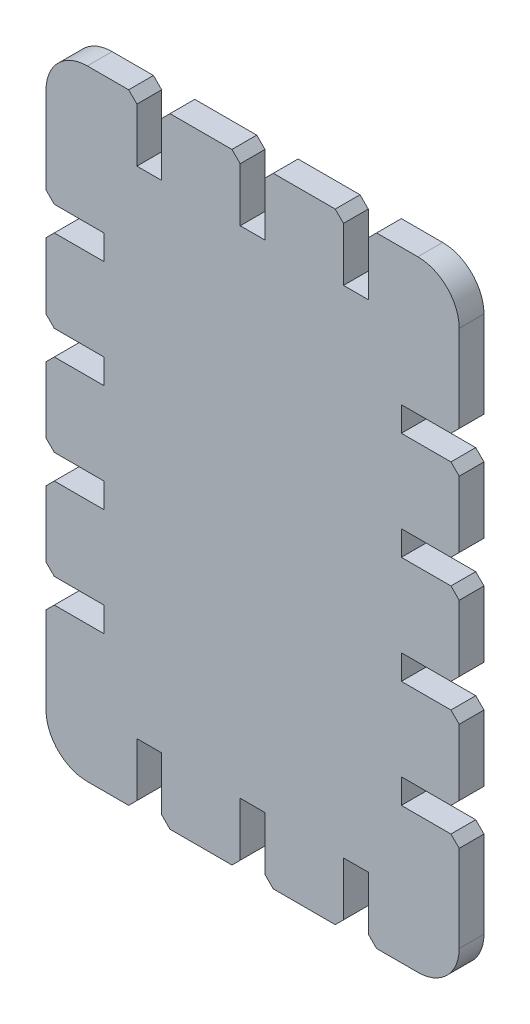
SolidWorks part; units mm, degrees
ref_plane "Front Plane" through (0, 0, 0) normal (0, 0, 1) x (1, 0, 0)
ref_plane "Top Plane" through (0, 0, 0) normal (0, 1, 0) x (1, 0, 0)
ref_plane "Right Plane" through (0, 0, 0) normal (1, 0, 0) x (0, 0, -1)
sketch "Sketch1" plane through (0, 0, 0) normal (0, 0, 1) x (1, 0, 0)
  line L0 (-5.5, 27.6932) -> (-5.5, -47.3068) construction
  line L1 (-15.5, 27.6932) -> (-8, 27.6932)
  line L2 (-25.5, -47.3068) -> (-20.5, -47.3068)
  line L3 (-30.5, -42.3068) -> (-30.5, -31.8068)
  line L4 (-25.5, 27.6932) -> (-20.5, 27.6932)
  line L5 (19.5, -42.3068) -> (19.5, -31.8068)
  line L6 (-30.5, -47.3068) -> (19.5, 27.6932) construction
  line L7 (-30.5, 27.6932) -> (19.5, -47.3068) construction
  line L8 (-16.5, 20.1932) -> (-19.5, 20.1932)
  line L9 (-16.5, 20.1932) -> (-16.5, 26.6932)
  line L10 (-20.5, 27.6932) -> (-19.5, 26.6932)
  line L11 (-19.5, 20.1932) -> (-19.5, 26.6932)
  line L12 (-16.5, 26.6932) -> (-15.5, 27.6932)
  line L13 (-4, 20.1932) -> (-7, 20.1932)
  line L14 (-4, 20.1932) -> (-4, 26.6932)
  line L15 (-7, 20.1932) -> (-7, 26.6932)
  line L16 (-8, 27.6932) -> (-7, 26.6932)
  line L17 (-4, 26.6932) -> (-3, 27.6932)
  line L18 (8.5, 20.1932) -> (5.5, 20.1932)
  line L19 (8.5, 20.1932) -> (8.5, 26.6932)
  line L20 (5.5, 20.1932) -> (5.5, 26.6932)
  line L21 (4.5, 27.6932) -> (5.5, 26.6932)
  line L22 (8.5, 26.6932) -> (9.5, 27.6932)
  line L23 (-3, 27.6932) -> (4.5, 27.6932)
  line L24 (9.5, 27.6932) -> (14.5, 27.6932)
  line L25 (12.5, 11.1932) -> (18.5, 11.1932)
  line L26 (12.5, 11.1932) -> (12.5, 8.1932)
  line L27 (12.5, 8.1932) -> (18.5, 8.1932)
  line L28 (19.5, 12.1932) -> (19.5, 22.6932)
  line L29 (18.5, 11.1932) -> (19.5, 12.1932)
  line L30 (18.5, 8.1932) -> (19.5, 7.1932)
  line L31 (-30.5, -9.8068) -> (19.5, -9.8068) construction
  line L32 (8.5, -46.3068) -> (9.5, -47.3068)
  line L33 (4.5, -47.3068) -> (5.5, -46.3068)
  line L34 (5.5, -39.8068) -> (5.5, -46.3068)
  line L35 (8.5, -39.8068) -> (8.5, -46.3068)
  line L36 (8.5, -39.8068) -> (5.5, -39.8068)
  line L37 (-4, -46.3068) -> (-3, -47.3068)
  line L38 (-8, -47.3068) -> (-7, -46.3068)
  line L39 (-7, -39.8068) -> (-7, -46.3068)
  line L40 (-4, -39.8068) -> (-4, -46.3068)
  line L41 (-4, -39.8068) -> (-7, -39.8068)
  line L42 (-16.5, -46.3068) -> (-15.5, -47.3068)
  line L43 (-19.5, -39.8068) -> (-19.5, -46.3068)
  line L44 (-20.5, -47.3068) -> (-19.5, -46.3068)
  line L45 (-16.5, -39.8068) -> (-16.5, -46.3068)
  line L46 (-16.5, -39.8068) -> (-19.5, -39.8068)
  line L47 (-15.5, -47.3068) -> (-8, -47.3068)
  line L48 (-3, -47.3068) -> (4.5, -47.3068)
  line L49 (12.5, -1.8068) -> (18.5, -1.8068)
  line L50 (12.5, -1.8068) -> (12.5, -4.8068)
  line L51 (12.5, -4.8068) -> (18.5, -4.8068)
  line L52 (18.5, -1.8068) -> (19.5, -0.8068)
  line L53 (18.5, -4.8068) -> (19.5, -5.8068)
  line L54 (12.5, -14.8068) -> (18.5, -14.8068)
  line L55 (12.5, -14.8068) -> (12.5, -17.8068)
  line L56 (12.5, -17.8068) -> (18.5, -17.8068)
  line L57 (18.5, -14.8068) -> (19.5, -13.8068)
  line L58 (18.5, -17.8068) -> (19.5, -18.8068)
  line L59 (12.5, -27.8068) -> (18.5, -27.8068)
  line L60 (12.5, -27.8068) -> (12.5, -30.8068)
  line L61 (12.5, -30.8068) -> (18.5, -30.8068)
  line L62 (18.5, -27.8068) -> (19.5, -26.8068)
  line L63 (18.5, -30.8068) -> (19.5, -31.8068)
  line L64 (19.5, -0.8068) -> (19.5, 7.1932)
  line L65 (19.5, -13.8068) -> (19.5, -5.8068)
  line L66 (19.5, -26.8068) -> (19.5, -18.8068)
  line L67 (-23.5, -27.8068) -> (-23.5, -30.8068)
  line L68 (-23.5, -14.8068) -> (-23.5, -17.8068)
  line L69 (-23.5, -1.8068) -> (-23.5, -4.8068)
  line L70 (-29.5, 11.1932) -> (-30.5, 12.1932)
  line L71 (-23.5, 11.1932) -> (-23.5, 8.1932)
  line L72 (-23.5, 11.1932) -> (-29.5, 11.1932)
  line L73 (-29.5, -4.8068) -> (-30.5, -5.8068)
  line L74 (-29.5, -1.8068) -> (-30.5, -0.8068)
  line L75 (-23.5, -4.8068) -> (-29.5, -4.8068)
  line L76 (-23.5, -1.8068) -> (-29.5, -1.8068)
  line L77 (-29.5, 8.1932) -> (-30.5, 7.1932)
  line L78 (-23.5, 8.1932) -> (-29.5, 8.1932)
  line L79 (-29.5, -30.8068) -> (-30.5, -31.8068)
  line L80 (-29.5, -27.8068) -> (-30.5, -26.8068)
  line L81 (-23.5, -30.8068) -> (-29.5, -30.8068)
  line L82 (-23.5, -27.8068) -> (-29.5, -27.8068)
  line L83 (-29.5, -17.8068) -> (-30.5, -18.8068)
  line L84 (-29.5, -14.8068) -> (-30.5, -13.8068)
  line L85 (-23.5, -17.8068) -> (-29.5, -17.8068)
  line L86 (-23.5, -14.8068) -> (-29.5, -14.8068)
  line L87 (-30.5, 12.1932) -> (-30.5, 22.6932)
  line L88 (-30.5, -0.8068) -> (-30.5, 7.1932)
  line L89 (-30.5, -13.8068) -> (-30.5, -5.8068)
  line L90 (-30.5, -26.8068) -> (-30.5, -18.8068)
  line L91 (-18, 27.6932) -> (-18, 17.7664) construction
  line L92 (9.5, -47.3068) -> (14.5, -47.3068)
  line L93 (19.5, 9.6932) -> (12.5, 9.6932) construction
  arc A0 (14.5, -47.3068) -> (19.5, -42.3068) centre (14.5, -42.3068) ccw
  arc A1 (-25.5, -47.3068) -> (-30.5, -42.3068) centre (-25.5, -42.3068) cw
  arc A2 (19.5, 22.6932) -> (14.5, 27.6932) centre (14.5, 22.6932) ccw
  arc A3 (-30.5, 22.6932) -> (-25.5, 27.6932) centre (-25.5, 22.6932) cw
  point P0 (-5.5, -9.8068)
  point P4 (0, 0)
  point P9 (-18, 27.6932)
  point P10 (-16.5, 27.6932)
  point P14 (-19.5, 27.6932)
  point P21 (-5.5, 27.6932)
  point P22 (-4, 27.6932)
  point P26 (-7, 27.6932)
  point P30 (7, 27.6932)
  point P31 (8.5, 27.6932)
  point P35 (5.5, 27.6932)
  point P46 (19.5, 9.6932)
  point P50 (19.5, 8.1932)
  point P51 (19.5, 11.1932)
  point P121 (-18, 20.1932)
  point P124 (12.5, -29.3068)
  dimension "D3" = 5
  dimension "D1" = 3
  dimension "D2" = 12.5
  dimension "D4" = 18
  dimension "D5" = 4
  dimension "D6" = 3
  dimension "D11" = 3
  dimension "D12" = 18
extrude "Boss-Extrude1" add sketch "Sketch1" along normal blind 3 contours L87 A3 L4 L10 L11 L8 L9 L12 L1 L16 L15 L13 L14 L17 L23 L21 L20 L18 L19 L22 L24 A2 L28 L29 L25 L26 L27 L30 L64 L52 L49 L50 L51 L53 L65 L57 L54 L55 L56 L58 L66 L62 L59 L60 L61 L63 L5 A0 L92 L32 L35 L36 L34 L33 L48 L37 L40 L41 L39 L38 L47 L42 L45 L46 L43 L44 L2 A1 L3 L79 L81 L67 L82 L80 L90 L83 L85 L68 L86 L84 L89 L73 L75 L69 L76 L74 L88 L77 L78 L71 L72 L70
